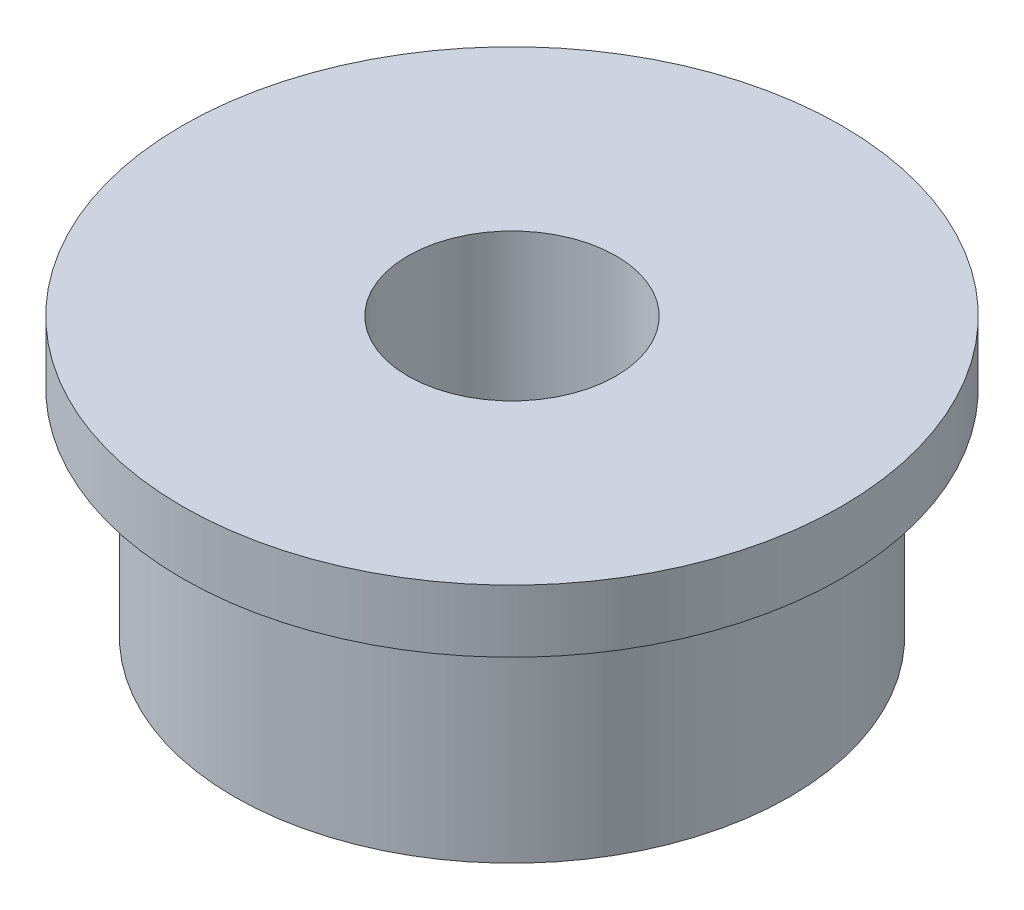
SolidWorks part; units mm, degrees
ref_plane "Front Plane" through (0, 0, 0) normal (0, 0, 1) x (1, 0, 0)
ref_plane "Top Plane" through (0, 0, 0) normal (0, 1, 0) x (1, 0, 0)
ref_plane "Right Plane" through (0, 0, 0) normal (1, 0, 0) x (0, 0, -1)
sketch "Sketch1" plane through (0, 0, 0) normal (0, 1, 0) x (1, 0, 0)
  circle A0 centre (0, 0) radius 4
  circle A1 centre (0, 0) radius 1.5
  dimension "D1" = 3
  dimension "D2" = 8
extrude "Boss-Extrude1" add sketch "Sketch1" along normal blind 4
sketch "Sketch2" plane through (0, 4, 0) normal (0, 1, 0) x (1, 0, 0)
  circle A0 centre (0, 0) radius 4.75
  circle A1 centre (0, 0) radius 1.5
  dimension "D1" = 9.5
extrude "Boss-Extrude2" add sketch "Sketch2" against normal blind 0.9
